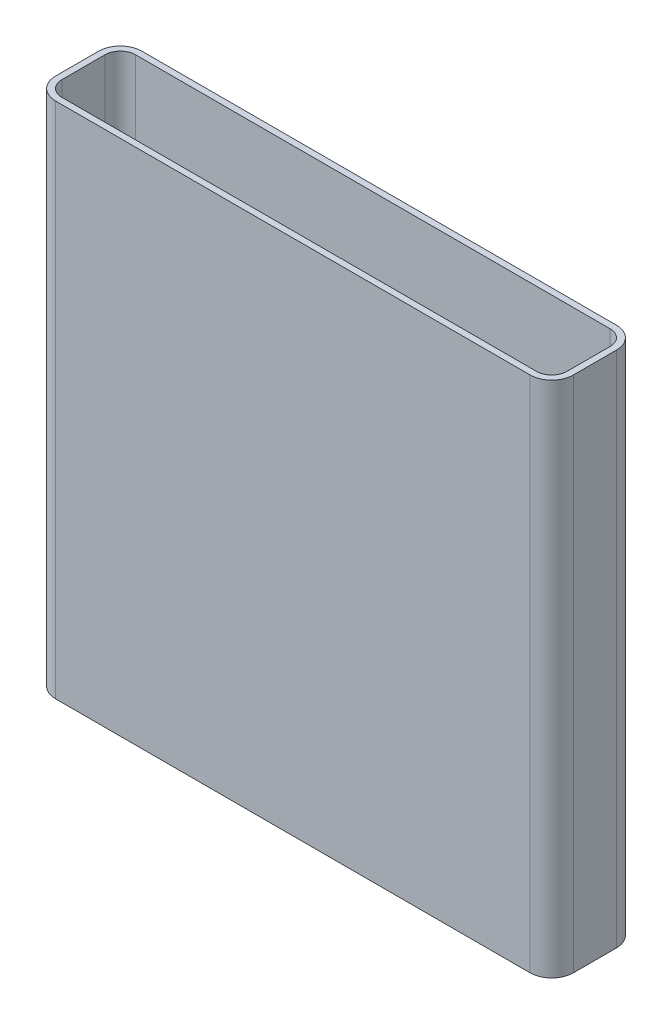
SolidWorks part; units mm, degrees
ref_plane "Front Plane" through (0, 0, 0) normal (0, 0, 1) x (1, 0, 0)
ref_plane "Top Plane" through (0, 0, 0) normal (0, 1, 0) x (1, 0, 0)
ref_plane "Right Plane" through (0, 0, 0) normal (1, 0, 0) x (0, 0, -1)
sketch "Sketch1" plane through (0, 0, 0) normal (0, 1, 0) x (1, 0, 0)
  line L1 (-838.2, 152.4) -> (838.2, 152.4)
  line L2 (-914.4, 76.2) -> (-914.4, -76.2)
  line L3 (-838.2, -152.4) -> (838.2, -152.4)
  line L4 (914.4, 76.2) -> (914.4, -76.2)
  line L5 (-914.4, 152.4) -> (914.4, -152.4) construction
  line L6 (-914.4, -152.4) -> (914.4, 152.4) construction
  arc A0 (838.2, 152.4) -> (914.4, 76.2) centre (838.2, 76.2) cw
  arc A1 (838.2, -152.4) -> (914.4, -76.2) centre (838.2, -76.2) ccw
  arc A2 (-914.4, -76.2) -> (-838.2, -152.4) centre (-838.2, -76.2) ccw
  arc A3 (-838.2, 152.4) -> (-914.4, 76.2) centre (-838.2, 76.2) ccw
  point P0 (0, 0)
  dimension "D3" = 76.2
  dimension "D1" = 304.8
  dimension "D2" = 1828.8
extrude "Extrude-Thin1" add sketch "Sketch1" along normal blind 1828.8 thin
